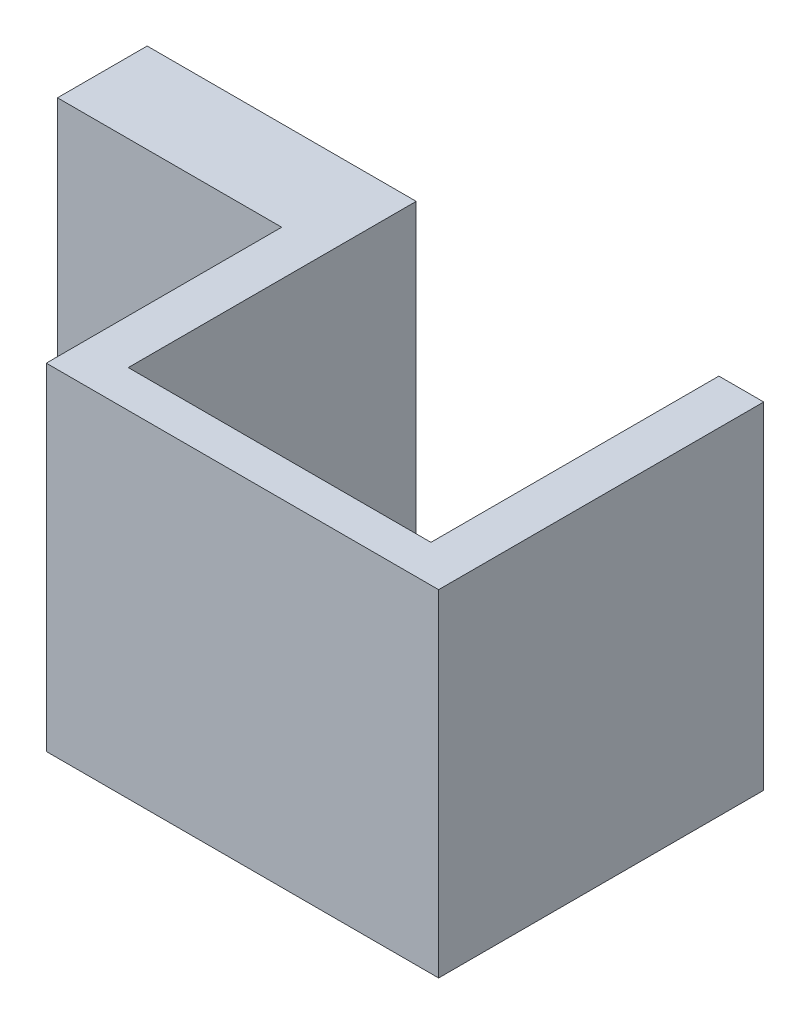
SolidWorks part; units mm, degrees
ref_plane "Front Plane" through (0, 0, 0) normal (0, 0, 1) x (1, 0, 0)
ref_plane "Top Plane" through (0, 0, 0) normal (0, 1, 0) x (1, 0, 0)
ref_plane "Right Plane" through (0, 0, 0) normal (1, 0, 0) x (0, 0, -1)
sketch "Croquis1" plane through (0, 0, 0) normal (0, 1, 0) x (1, 0, 0)
  line L0 (-8.75, -7.25) -> (-8.75, 7.25)
  line L1 (-8.75, -7.25) -> (8.75, -7.25)
  line L2 (-8.75, 7.25) -> (8.75, 7.25)
  line L3 (8.75, -7.25) -> (8.75, 7.25)
  line L4 (-8.75, -7.25) -> (8.75, 7.25) construction
  line L5 (-8.75, 7.25) -> (8.75, -7.25) construction
  line L6 (-6.75, 7.25) -> (-6.75, -5.5929)
  line L7 (-6.75, -5.5929) -> (6.75, -5.5929)
  line L8 (6.75, -5.5929) -> (6.75, 7.25)
  line L9 (-8.75, 7.25) -> (-18.75, 7.25)
  line L10 (-18.75, 7.25) -> (-18.75, 3.25)
  line L11 (-18.75, 3.25) -> (-8.75, 3.25)
  point P1 (0, 0)
  dimension "D1" = 14.5
  dimension "D2" = 17.5
  dimension "D3" = 2
  dimension "D4" = 4
  dimension "D5" = 10
extrude "Saliente-Extruir1" add sketch "Croquis1" along normal blind 15 contours L8 L7 L6 L2 L0 L1 L3 | L10 L11 L0 L9
sketch "Croquis2" plane through (0, 0, -3.25) normal (0, 0, 1) x (1, 0, 0)
  line L0 (-18.75, 15) -> (-8.75, 15) construction
  line L1 (-18.75, 15) -> (-18.75, 0) construction
  circle A0 centre (-13.75, 7.5) radius 1.5
  dimension "D1" = 3
  dimension "D2" = 7.5
  dimension "D3" = 5
extrude "Cortar-Extruir1" cut sketch "Croquis2" against normal blind 15
